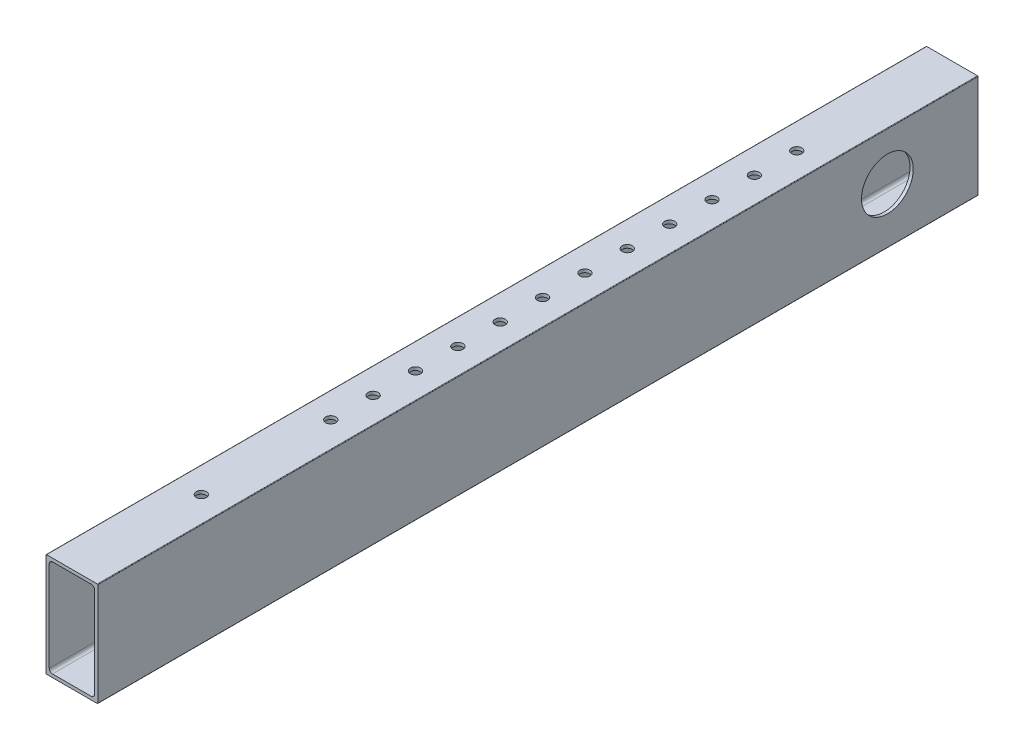
SolidWorks part; units mm, degrees
material "6061 Alloy"
ref_plane "Front Plane" through (0, 0, 0) normal (0, 0, 1) x (1, 0, 0)
ref_plane "Top Plane" through (0, 0, 0) normal (0, 1, 0) x (1, 0, 0)
ref_plane "Right Plane" through (0, 0, 0) normal (1, 0, 0) x (0, 0, -1)
ref_plane "Plane1" through (0, 0, 0) normal (0, 0, -1) x (-1, 0, 0)
sketch "Sketch1" plane through (0, 0, 0) normal (0, 0, -1) x (-1, 0, 0)
  line L0 (-11.1125, -22.225) -> (-11.1125, 22.225)
  line L1 (-9.525, 23.8125) -> (9.525, 23.8125)
  line L2 (11.1125, 22.225) -> (11.1125, -22.225)
  line L3 (9.525, -23.8125) -> (-9.525, -23.8125)
  line L4 (-12.7, 25.146) -> (-12.7, -25.146)
  line L5 (-12.446, -25.4) -> (12.446, -25.4)
  line L6 (12.7, -25.146) -> (12.7, 25.146)
  line L7 (12.446, 25.4) -> (-12.446, 25.4)
  arc A0 (-11.1125, 22.225) -> (-9.525, 23.8125) centre (-9.525, 22.225) cw
  arc A1 (9.525, 23.8125) -> (11.1125, 22.225) centre (9.525, 22.225) cw
  arc A2 (11.1125, -22.225) -> (9.525, -23.8125) centre (9.525, -22.225) cw
  arc A3 (-9.525, -23.8125) -> (-11.1125, -22.225) centre (-9.525, -22.225) cw
  arc A4 (-12.7, -25.146) -> (-12.446, -25.4) centre (-12.446, -25.146) ccw
  arc A5 (12.446, -25.4) -> (12.7, -25.146) centre (12.446, -25.146) ccw
  arc A6 (12.7, 25.146) -> (12.446, 25.4) centre (12.446, 25.146) ccw
  arc A7 (-12.446, 25.4) -> (-12.7, 25.146) centre (-12.446, 25.146) ccw
extrude "Boss-Extrude1" add sketch "Sketch1" against normal blind 406.4 and the other way blind 25.4
sketch "Sketch2" plane through (-12.7, 0, 0) normal (-1, 0, 0) x (0, 0, 1)
  line L0 (0, 1.778) -> (19.05, 1.778) construction
  line L1 (0, 25.146) -> (0, -25.146) construction
  line L8 (-25.4, 25.146) -> (406.4, 25.146) construction
  line L9 (-25.4, -25.146) -> (406.4, -25.146) construction
  line L10 (-25.4, -25.4) -> (406.4, -25.4) construction
  circle A0 centre (19.05, 1.778) radius 12.7
  dimension "D3" = 27.178
  dimension "D2" = 25.4
  dimension "D1" = 19.05
extrude "Cut-Extrude1" cut sketch "Sketch2" against normal blind 25.4
sketch "Sketch3" plane through (0, -25.4, 0) normal (0, -1, 0) x (1, 0, 0)
  line L0 (0, 0) -> (0, 406.4) construction
  line L1 (12.446, 406.4) -> (-12.446, 406.4) construction
  line L2 (12.446, -25.4) -> (-12.446, -25.4) construction
  circle A0 centre (0, 50.8) radius 2.4892
  circle A1 centre (0, 71.5818) radius 2.4892
  circle A2 centre (0, 92.3636) radius 2.4892
  circle A3 centre (0, 113.1455) radius 2.4892
  circle A4 centre (0, 133.9273) radius 2.4892
  circle A5 centre (0, 154.7091) radius 2.4892
  circle A6 centre (0, 175.4909) radius 2.4892
  circle A7 centre (0, 196.2727) radius 2.4892
  circle A8 centre (0, 217.0545) radius 2.4892
  circle A9 centre (0, 237.8364) radius 2.4892
  circle A10 centre (0, 258.6182) radius 2.4892
  circle A11 centre (0, 342.9) radius 2.4892
  circle A13 centre (0, 279.4) radius 2.4892
  dimension "D1" = 76.2
  dimension "D2" = 4.9784
  dimension "D3" = 12
  dimension "D4" = 4.9784
  dimension "D7" = 127
  dimension "D5" = 63.5
extrude "Cut-Extrude2" cut sketch "Sketch3" against normal through all both
